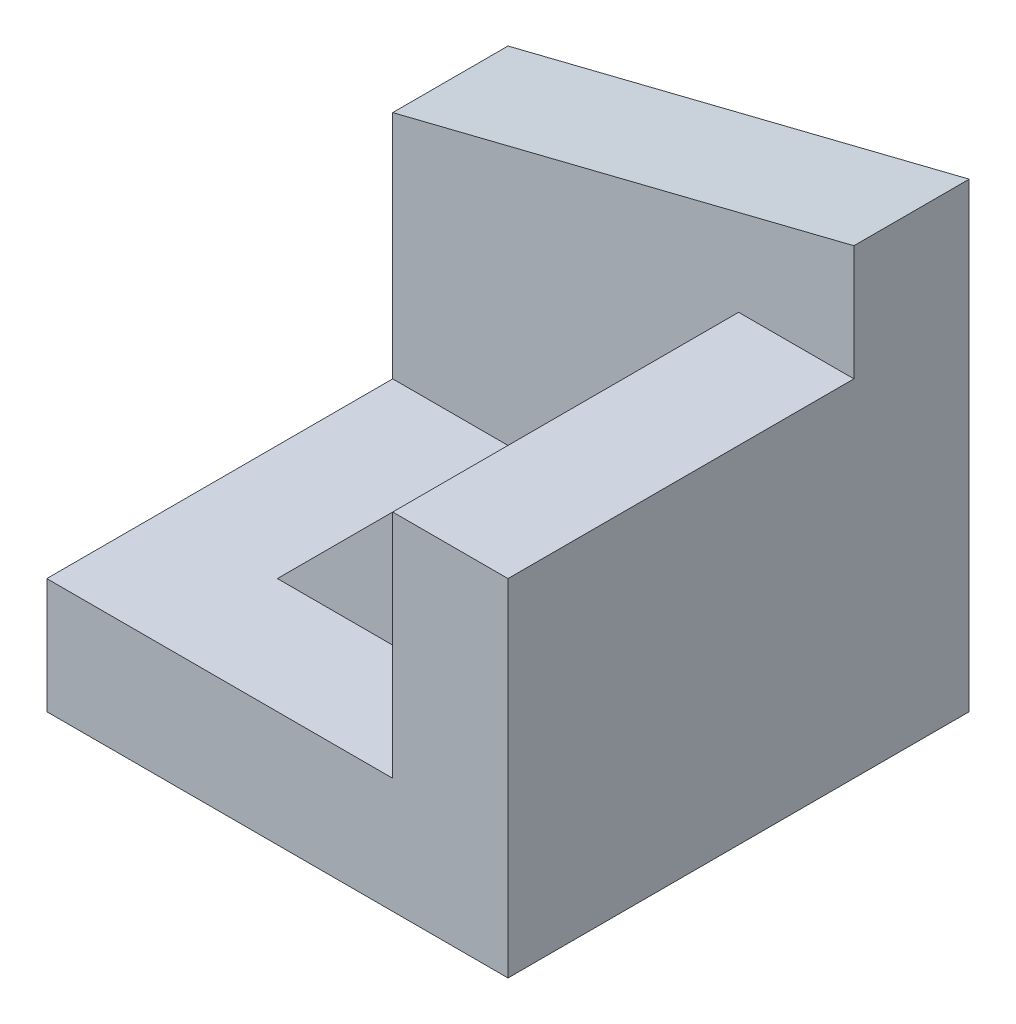
SolidWorks part; units mm, degrees
ref_plane "Front Plane" through (0, 0, 0) normal (0, 0, 1) x (1, 0, 0)
ref_plane "Top Plane" through (0, 0, 0) normal (0, 1, 0) x (1, 0, 0)
ref_plane "Right Plane" through (0, 0, 0) normal (1, 0, 0) x (0, 0, -1)
sketch "Sketch1" plane through (0, 0, 0) normal (0, 0, 1) x (1, 0, 0)
  line L1 (0, 0) -> (40, 0)
  line L2 (0, 0) -> (0, 40)
  line L3 (0, 40) -> (40, 40)
  line L4 (40, 0) -> (40, 40)
  dimension "D1" = 40
  dimension "D2" = 40
extrude "Boss-Extrude1" add sketch "Sketch1" along normal blind 40
sketch "Sketch2" plane through (0, 0, 40) normal (0, 0, 1) x (1, 0, 0)
  line L0 (40, 40) -> (0, 30)
  line L1 (0, 40) -> (0, 0) construction
  line L2 (0, 30) -> (0, 40)
  line L3 (0, 40) -> (40, 40)
  dimension "D1" = 10
extrude "Cut-Extrude1" cut sketch "Sketch2" against normal blind 40
sketch "Sketch3" plane through (40, 0, 0) normal (1, 0, 0) x (0, 0, -1)
  line L1 (-40, 40) -> (-10, 40)
  line L2 (-40, 40) -> (-40, 30)
  line L3 (-40, 30) -> (-10, 30)
  line L4 (-10, 40) -> (-10, 30)
  dimension "D1" = 30
  dimension "D2" = 10
extrude "Cut-Extrude2" cut sketch "Sketch3" against normal blind 40
sketch "Sketch4" plane through (0, 0, 40) normal (0, 0, 1) x (1, 0, 0)
  line L0 (30, 30) -> (10, 10)
  line L1 (0, 30) -> (40, 30) construction
  line L2 (10, 10) -> (30, 10)
  line L3 (30, 10) -> (30, 30)
  line L4 (40, 0) -> (40, 30) construction
  line L5 (30, 30) -> (10, 30)
  line L6 (10, 30) -> (10, 10)
  dimension "D1" = 20
  dimension "D2" = 10
  dimension "D3" = 20
  dimension "D4" = 0
extrude "Cut-Extrude6" cut sketch "Sketch4" against normal blind 30 contours L5 L6 L0
sketch "Sketch6" plane through (10, 0, 0) normal (1, 0, 0) x (0, 0, -1)
  line L1 (-10, 30) -> (-40, 30)
  line L2 (-10, 30) -> (-10, 10)
  line L3 (-10, 10) -> (-40, 10)
  line L4 (-40, 30) -> (-40, 10)
  dimension "D1" = 30
  dimension "D2" = 20
extrude "Cut-Extrude7" cut sketch "Sketch6" against normal blind 30
sketch "Sketch7" plane through (0, 0, 40) normal (0, 0, 1) x (1, 0, 0)
  line L0 (10, 10) -> (30, 10)
  line L1 (30, 30) -> (30, 10)
  line L2 (30, 10) -> (30, 30)
  line L3 (10, 10) -> (30, 30)
  line M1 (30, 30) -> (10, 10)
extrude "Cut-Extrude9" cut sketch "Sketch7" against normal blind 10 contours L1 L0 M1
